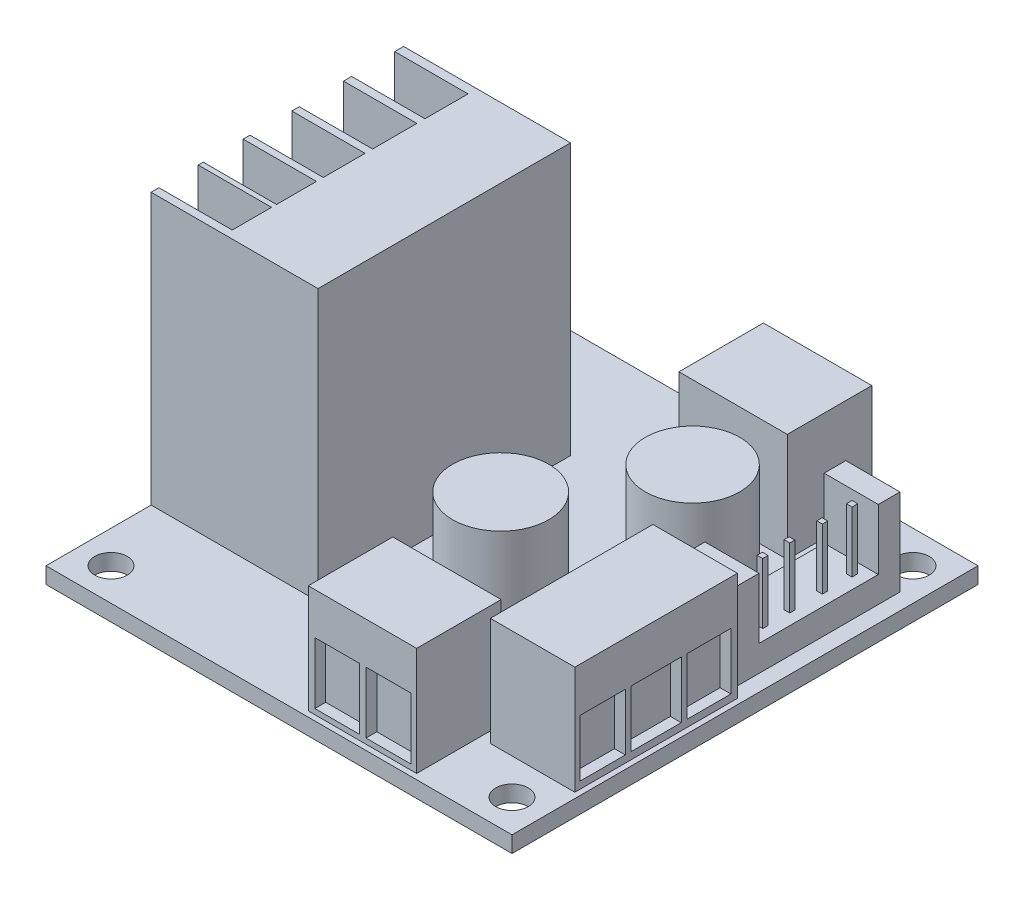
SolidWorks part; units mm, degrees
ref_plane "Front" through (0, 0, 0) normal (0, 0, 1) x (1, 0, 0)
ref_plane "Top" through (0, 0, 0) normal (0, 1, 0) x (1, 0, 0)
ref_plane "Right" through (0, 0, 0) normal (1, 0, 0) x (0, 0, -1)
sketch "草圖1" plane through (0, 0, 0) normal (0, 1, 0) x (1, 0, 0)
  line L0 (43, 21.5) -> (0, 21.5) construction
  line L1 (0, 0) -> (43, 0)
  line L2 (0, 0) -> (0, 43)
  line L3 (0, 43) -> (43, 43)
  line L4 (43, 0) -> (43, 43)
  dimension "D1" = 43
  dimension "D2" = 43
extrude "填料-伸長1" add sketch "草圖1" along normal blind 1.5
sketch "草圖2" plane through (0, 1.5, 0) normal (0, 1, 0) x (1, 0, 0)
  line L0 (43, 0) -> (43, 43) construction
  line L1 (34.7, 21.3) -> (42.5, 21.3)
  line L2 (34.7, 21.3) -> (34.7, 6.3)
  line L3 (34.7, 6.3) -> (42.5, 6.3)
  line L4 (42.5, 21.3) -> (42.5, 6.3)
  line L5 (23.7, 8.3) -> (33.7, 8.3)
  line L6 (23.7, 8.3) -> (23.7, 0.5)
  line L7 (23.7, 0.5) -> (33.7, 0.5)
  line L8 (33.7, 8.3) -> (33.7, 0.5)
  line L9 (23.7, 34.7) -> (33.7, 34.7)
  line L10 (23.7, 34.7) -> (23.7, 42.5)
  line L11 (23.7, 42.5) -> (33.7, 42.5)
  line L12 (33.7, 34.7) -> (33.7, 42.5)
  line L13 (0, 0) -> (43, 0) construction
  line L14 (43, 43) -> (0, 43) construction
  dimension "D1" = 15
  dimension "D2" = 7.8
  dimension "D3" = 7.8
  dimension "D4" = 10
  dimension "D5" = 10
  dimension "D6" = 7.8
  dimension "D7" = 0.5
  dimension "D8" = 6.3
  dimension "D9" = 9.3
  dimension "D10" = 0.5
  dimension "D11" = 0.5
  dimension "D12" = 9.3
extrude "填料-伸長2" add sketch "草圖2" along normal blind 10 separate body
sketch "草圖3" plane through (0, 1.5, 0) normal (0, 1, 0) x (1, 0, 0)
  line L0 (0, 43) -> (0, 0) construction
  line L1 (0, 9.7) -> (15.4, 9.7)
  line L2 (0, 9.7) -> (0, 33)
  line L3 (0, 33) -> (15.4, 33)
  line L4 (15.4, 9.7) -> (15.4, 33)
  line L5 (43, 43) -> (0, 43) construction
  dimension "D1" = 23.3
  dimension "D2" = 10
  dimension "D3" = 15.4
extrude "填料-伸長3" add sketch "草圖3" along normal blind 25 separate body
sketch "草圖4" plane through (0, 26.5, 0) normal (0, 1, 0) x (1, 0, 0)
  line L0 (0, 33) -> (0, 9.7) construction
  line L1 (0, 32.1773) -> (6.7647, 32.1773)
  line L2 (0, 32.1773) -> (0, 28.2057)
  line L3 (0, 28.2057) -> (6.7647, 28.2057)
  line L4 (6.7647, 32.1773) -> (6.7647, 28.2057)
  line L6 (0, 27.4574) -> (6.7647, 27.4574)
  line L7 (0, 27.4574) -> (0, 23.3707)
  line L8 (0, 23.3707) -> (6.7647, 23.3707)
  line L9 (6.7647, 27.4574) -> (6.7647, 23.3707)
  line L10 (0, 22.68) -> (6.7647, 22.68)
  line L11 (0, 22.68) -> (0, 18.8235)
  line L12 (0, 18.8235) -> (6.7647, 18.8235)
  line L13 (6.7647, 22.68) -> (6.7647, 18.8235)
  line L14 (0, 18.1903) -> (6.7647, 18.1903)
  line L15 (0, 18.1903) -> (0, 14.5065)
  line L16 (0, 14.5065) -> (6.7647, 14.5065)
  line L17 (6.7647, 18.1903) -> (6.7647, 14.5065)
  line L18 (0, 14.046) -> (6.7647, 14.046)
  line L19 (0, 14.046) -> (0, 10.4197)
  line L20 (0, 10.4197) -> (6.7647, 10.4197)
  line L21 (6.7647, 14.046) -> (6.7647, 10.4197)
extrude "除料-伸長1" cut sketch "草圖4" against normal blind 25
sketch "草圖5" plane through (0, 1.5, 0) normal (0, 1, 0) x (1, 0, 0)
  circle A0 centre (31.7447, 27.9154) radius 4.3594
  circle A1 centre (25.0807, 16.875) radius 4.4359
extrude "填料-伸長4" add sketch "草圖5" along normal blind 10 separate body
sketch "草圖6" plane through (42.5, 0, 0) normal (1, 0, 0) x (0, 0, -1)
  line L1 (6.7778, 7.4011) -> (10.9587, 7.4011)
  line L2 (6.7778, 7.4011) -> (6.7778, 2.1527)
  line L3 (6.7778, 2.1527) -> (10.9587, 2.1527)
  line L4 (10.9587, 7.4011) -> (10.9587, 2.1527)
  line L5 (11.4925, 7.4011) -> (16.1182, 7.4011)
  line L6 (11.4925, 7.4011) -> (11.4925, 2.1527)
  line L7 (11.4925, 2.1527) -> (16.1182, 2.1527)
  line L8 (16.1182, 7.4011) -> (16.1182, 2.1527)
  line L9 (16.6519, 7.4011) -> (20.6994, 7.4011)
  line L10 (16.6519, 7.4011) -> (16.6519, 2.1527)
  line L11 (16.6519, 2.1527) -> (20.6994, 2.1527)
  line L12 (20.6994, 7.4011) -> (20.6994, 2.1527)
extrude "除料-伸長2" cut sketch "草圖6" against normal blind 1
sketch "草圖8" plane through (0, 0, -0.5) normal (0, 0, 1) x (1, 0, 0)
  line L1 (24.306, 7.6619) -> (28.4119, 7.6619)
  line L2 (24.306, 7.6619) -> (24.306, 1.9934)
  line L3 (24.306, 1.9934) -> (28.4119, 1.9934)
  line L4 (28.4119, 7.6619) -> (28.4119, 1.9934)
  line L5 (29.0247, 7.6619) -> (33.1612, 7.6619)
  line L6 (29.0247, 7.6619) -> (29.0247, 1.9934)
  line L7 (29.0247, 1.9934) -> (33.1612, 1.9934)
  line L8 (33.1612, 7.6619) -> (33.1612, 1.9934)
extrude "除料-伸長3" cut sketch "草圖8" against normal blind 1
sketch "草圖9" plane through (0, 0, -42.5) normal (0, 0, -1) x (-1, 0, 0)
  line L1 (-32.9885, 7.7613) -> (-28.7889, 7.7613)
  line L2 (-32.9885, 7.7613) -> (-32.9885, 2.1263)
  line L3 (-32.9885, 2.1263) -> (-28.7889, 2.1263)
  line L4 (-28.7889, 7.7613) -> (-28.7889, 2.1263)
  line L5 (-28.0978, 7.7613) -> (-24.3234, 7.7613)
  line L6 (-28.0978, 7.7613) -> (-28.0978, 2.1263)
  line L7 (-28.0978, 2.1263) -> (-24.3234, 2.1263)
  line L8 (-24.3234, 7.7613) -> (-24.3234, 2.1263)
extrude "除料-伸長4" cut sketch "草圖9" against normal blind 1
sketch "草圖10" plane through (0, 0, 0) normal (0, -1, 0) x (1, 0, 0)
  line L0 (0, 0) -> (43, 0) construction
  line L1 (3, -3) -> (40, -3) construction
  line L2 (3, -3) -> (3, -40) construction
  line L3 (3, -40) -> (40, -40) construction
  line L4 (40, -3) -> (40, -40) construction
  line L5 (0, -43) -> (0, 0) construction
  circle A0 centre (40, -3) radius 1.5
  circle A1 centre (3, -3) radius 1.5
  circle A2 centre (3, -40) radius 1.5
  circle A3 centre (40, -40) radius 1.5
  dimension "D3" = 3
  dimension "D1" = 37
  dimension "D2" = 37
  dimension "D4" = 3
  dimension "D5" = 3
extrude "除料-伸長5" cut sketch "草圖10" against normal blind 3
sketch "草圖11" plane through (0, 1.5, 0) normal (0, 1, 0) x (1, 0, 0)
  line L0 (43, 0) -> (43, 43) construction
  line L1 (36.5, 37.3) -> (41.5, 37.3)
  line L2 (36.5, 37.3) -> (36.5, 22.3)
  line L3 (36.5, 22.3) -> (41.5, 22.3)
  line L4 (41.5, 37.3) -> (41.5, 22.3)
  line L6 (42.5, 21.3) -> (34.7, 21.3) construction
  dimension "D1" = 15
  dimension "D2" = 5
  dimension "D3" = 1.5
  dimension "D4" = 1
extrude "填料-伸長5" add sketch "草圖11" along normal blind 2.4 separate body
sketch "草圖12" plane through (0, 3.9, 0) normal (0, 1, 0) x (1, 0, 0)
  line L1 (36.5, 37.3) -> (41.5, 37.3)
  line L2 (36.5, 37.3) -> (36.5, 35.3)
  line L3 (36.5, 35.3) -> (41.5, 35.3)
  line L4 (41.5, 37.3) -> (41.5, 35.3)
  line L5 (41.5, 22.3) -> (41.5, 37.3) construction
  line L6 (36.5, 22.3) -> (41.5, 22.3)
  line L7 (36.5, 22.3) -> (36.5, 24.3)
  line L8 (36.5, 24.3) -> (41.5, 24.3)
  line L9 (41.5, 22.3) -> (41.5, 24.3)
  dimension "D1" = 2
  dimension "D2" = 2
extrude "填料-伸長6" add sketch "草圖12" along normal blind 5.6
sketch "草圖13" plane through (0, 3.9, 0) normal (0, 1, 0) x (1, 0, 0)
  line L1 (39.9705, 34.4078) -> (40.4907, 34.4078)
  line L2 (39.9705, 34.4078) -> (39.9705, 33.8875)
  line L3 (39.9705, 33.8875) -> (40.4907, 33.8875)
  line L4 (40.4907, 34.4078) -> (40.4907, 33.8875)
  line L5 (39.9705, 31.6423) -> (40.4907, 31.6423)
  line L6 (39.9705, 31.6423) -> (39.9705, 31.1495)
  line L7 (39.9705, 31.1495) -> (40.4907, 31.1495)
  line L8 (40.4907, 31.6423) -> (40.4907, 31.1495)
  line L9 (39.9705, 28.6031) -> (40.4907, 28.6031)
  line L10 (39.9705, 28.6031) -> (39.9705, 28.1376)
  line L11 (39.9705, 28.1376) -> (40.4907, 28.1376)
  line L12 (40.4907, 28.6031) -> (40.4907, 28.1376)
  line L13 (39.9705, 26.1388) -> (40.4907, 26.1388)
  line L14 (39.9705, 26.1388) -> (39.9705, 25.646)
  line L15 (39.9705, 25.646) -> (40.4907, 25.646)
  line L16 (40.4907, 26.1388) -> (40.4907, 25.646)
extrude "填料-伸長7" add sketch "草圖13" along normal blind 5.6
